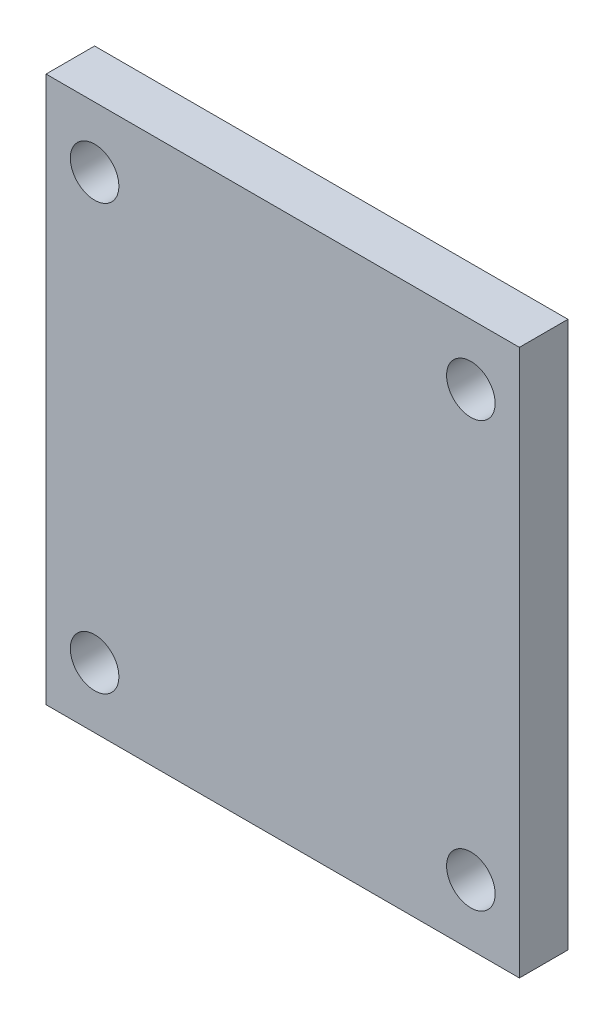
SolidWorks part; units mm, degrees
ref_plane "Front Plane" through (0, 0, 0) normal (0, 0, 1) x (1, 0, 0)
ref_plane "Top Plane" through (0, 0, 0) normal (0, 1, 0) x (1, 0, 0)
ref_plane "Right Plane" through (0, 0, 0) normal (1, 0, 0) x (0, 0, -1)
sketch "Sketch1" plane through (0, 0, 0) normal (0, 0, 1) x (1, 0, 0)
  line L0 (-19.8836, 22.4041) -> (-19.8836, -22.5959)
  line L1 (-19.8836, -22.5959) -> (19.1164, -22.5959)
  line L2 (19.1164, -22.5959) -> (19.1164, 22.4041)
  line L3 (19.1164, 22.4041) -> (-19.8836, 22.4041)
  circle A0 centre (-15.8836, -17.5959) radius 2
  circle A1 centre (15.1164, -17.5959) radius 2
  circle A2 centre (15.1164, 17.4041) radius 2
  circle A3 centre (-15.8836, 17.4041) radius 2
  dimension "D1" = 2
extrude "Boss-Extrude1" add sketch "Sketch1" along normal blind 4
